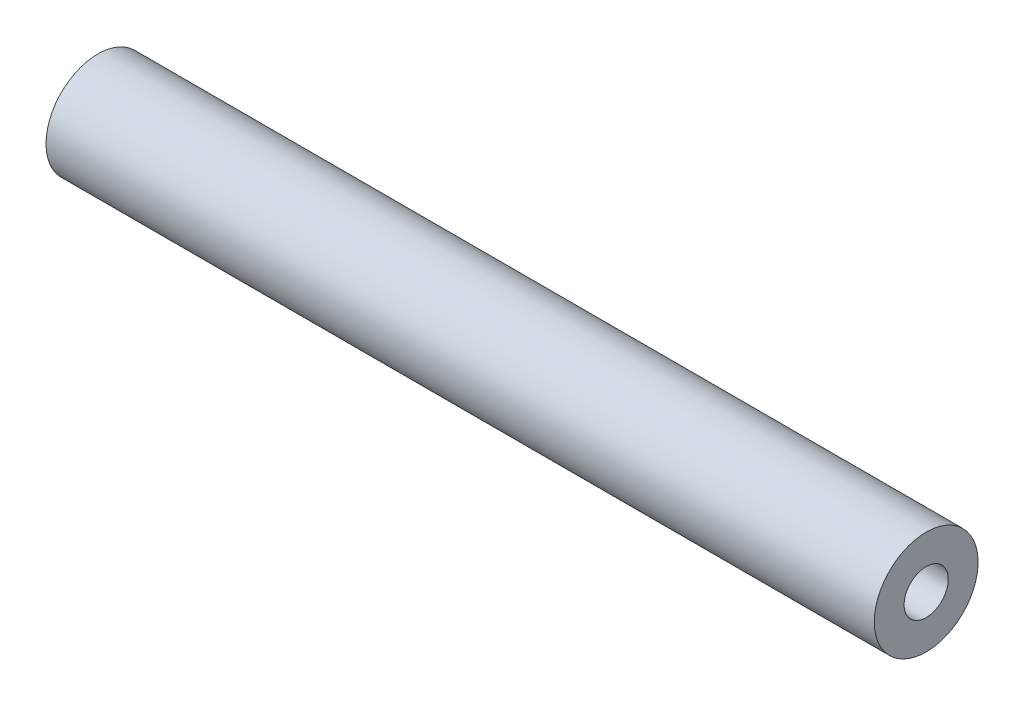
SolidWorks part; units mm, degrees
ref_plane "Front Plane" through (0, 0, 0) normal (0, 0, 1) x (1, 0, 0)
ref_plane "Top Plane" through (0, 0, 0) normal (0, 1, 0) x (1, 0, 0)
ref_plane "Right Plane" through (0, 0, 0) normal (1, 0, 0) x (0, 0, -1)
sketch "Sketch1" plane through (0, 0, 0) normal (0, 1, 0) x (1, 0, 0)
  line L0 (0, 0) -> (1.5582, 0) construction
  line L1 (0, 0.508) -> (19.05, 0.508)
  line L2 (0, 0.508) -> (0, 1.1938)
  line L3 (0, 1.1938) -> (19.05, 1.1938)
  line L4 (19.05, 0.508) -> (19.05, 1.1938)
  dimension "D1" = 2.3876
  dimension "D2" = 1.016
  dimension "D3" = 19.05
revolve "Revolve1" add sketch "Sketch1" angle 360 about L0
